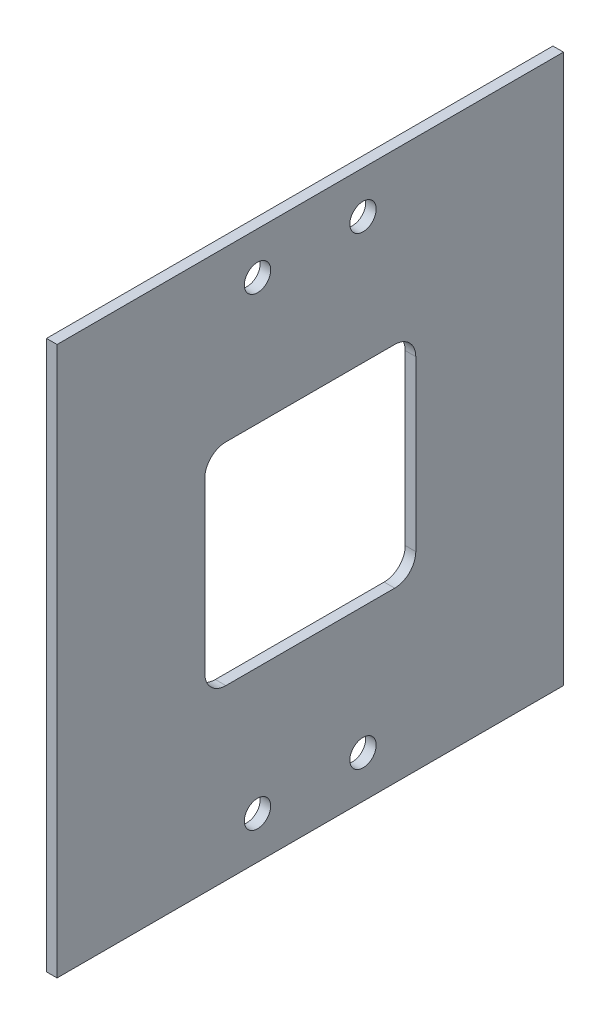
SolidWorks part; units mm, degrees
material "ASTM A36 Steel"
ref_plane "Front Plane" through (0, 0, 0) normal (0, 0, 1) x (1, 0, 0)
ref_plane "Top Plane" through (0, 0, 0) normal (0, 1, 0) x (1, 0, 0)
ref_plane "Right Plane" through (0, 0, 0) normal (1, 0, 0) x (0, 0, -1)
sketch "Sketch1" plane through (0, 0, 0) normal (1, 0, 0) x (0, 0, -1)
  line L0 (0, 2.6194) -> (0, -2.6194) construction
  line L1 (152.4, 82.55) -> (0, 82.55)
  line L2 (152.4, 82.55) -> (152.4, -82.55)
  line L3 (152.4, -82.55) -> (0, -82.55)
  line L4 (0, 82.55) -> (0, -82.55)
  line L5 (152.4, 82.55) -> (0, -82.55) construction
  line L6 (152.4, -82.55) -> (0, 82.55) construction
  line L7 (2.6194, 0) -> (-2.6194, 0) construction
  point P0 (76.2, 0)
  dimension "D1" = 152.4
  dimension "D2" = 165.1
extrude "Boss-Extrude1" add sketch "Sketch1" along normal blind 3.175
sketch "Sketch2" plane through (0, 0, 0) normal (-1, 0, 0) x (0, 0, 1)
  line L0 (-107.95, 25.4) -> (-107.95, -25.4)
  line L1 (-101.6, -31.75) -> (-50.8, -31.75)
  line L2 (-44.45, -25.4) -> (-44.45, 25.4)
  line L3 (-50.8, 31.75) -> (-101.6, 31.75)
  line L4 (-76.2, 31.75) -> (-76.2, -31.75) construction
  line L5 (0, 0) -> (-152.4, 0)
  line L6 (-152.4, -82.55) -> (-152.4, 82.55) construction
  arc A0 (-107.95, -25.4) -> (-101.6, -31.75) centre (-101.6, -25.4) ccw
  arc A1 (-50.8, -31.75) -> (-44.45, -25.4) centre (-50.8, -25.4) ccw
  arc A2 (-44.45, 25.4) -> (-50.8, 31.75) centre (-50.8, 25.4) ccw
  arc A3 (-101.6, 31.75) -> (-107.95, 25.4) centre (-101.6, 25.4) ccw
  point P19 (-76.2, 0)
  dimension "D1" = 6.35
  dimension "D2" = 63.5
  dimension "D3" = 63.5
extrude "Cut-Extrude1" cut sketch "Sketch2" against normal through all contours L4 L5 L0 A0 L1 | L4 L3 A3 L0 L5 | L3 L4 L5 L2 A2 | L5 L4 L1 A1 L2
sketch "Sketch3" plane through (0, 0, 0) normal (-1, 0, 0) x (0, 0, 1)
  line L0 (-76.2, 82.55) -> (-76.2, -82.55) construction
  line L1 (-152.4, 82.55) -> (0, 82.55) construction
  line L2 (0, -82.55) -> (-152.4, -82.55) construction
  line L3 (-92.075, -69.85) -> (-60.325, -69.85) construction
  line L4 (-92.075, 69.85) -> (-60.325, 69.85) construction
  circle A0 centre (-60.325, 69.85) radius 3.9687
  circle A1 centre (-92.075, 69.85) radius 3.9688
  circle A2 centre (-92.075, -69.85) radius 3.9687
  circle A3 centre (-60.325, -69.85) radius 3.9687
  point P10 (-76.2, 69.85)
  point P11 (-76.2, -69.85)
  dimension "D1" = 7.9375
  dimension "D2" = 12.7
  dimension "D3" = 31.75
  dimension "D4" = 12.7
extrude "Cut-Extrude2" cut sketch "Sketch3" against normal through all
sketch3d "TAG"
  line L0 (0, 82.55, -152.4) -> (0, 82.55, 0) construction
  line L1 (3.175, 82.55, 0) -> (0, 82.55, 0) construction
  line L2 (0, 82.55, 0) -> (0, -82.55, 0) construction
  line L3 (0, 82.55, -152.4) -> (0, 82.55, 0)
  line L4 (3.175, 82.55, 0) -> (0, 82.55, 0)
  line L5 (0, 82.55, 0) -> (0, -82.55, 0)
  dimension "D1" = 3.175
  dimension "D2" = 152.4
  dimension "D3" = 165.1
